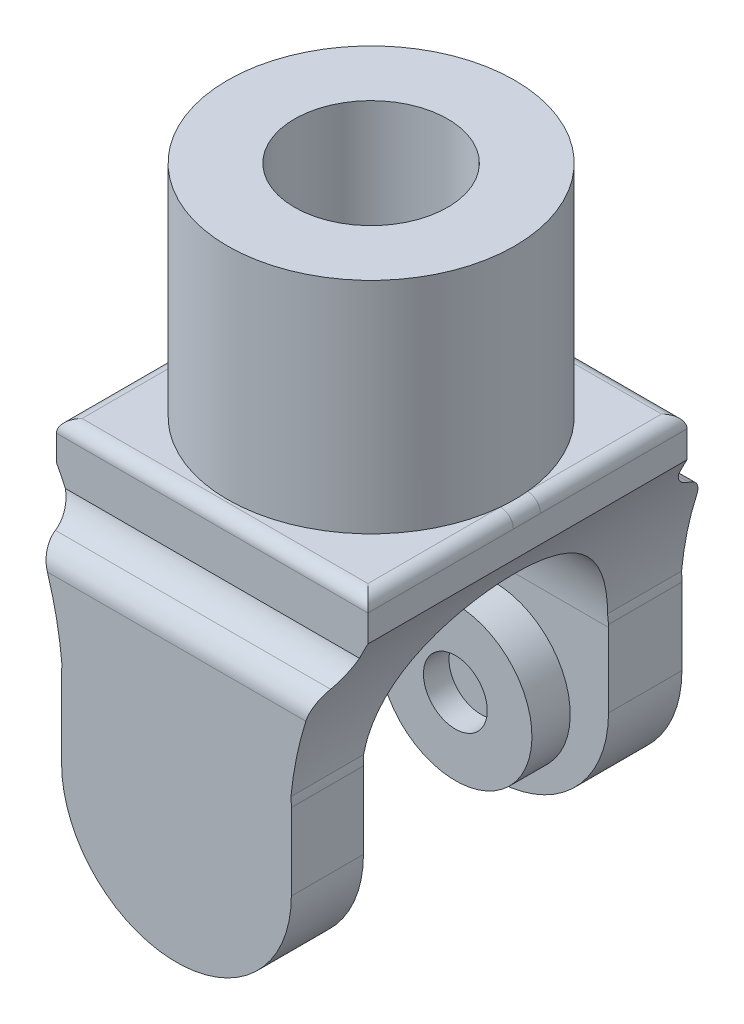
SolidWorks part; units mm, degrees
ref_plane "Front Plane" through (0, 0, 0) normal (0, 0, 1) x (1, 0, 0)
ref_plane "Top Plane" through (0, 0, 0) normal (0, 1, 0) x (1, 0, 0)
ref_plane "Right Plane" through (0, 0, 0) normal (1, 0, 0) x (0, 0, -1)
sketch "Sketch1" plane through (0, 0, 0) normal (0, 1, 0) x (1, 0, 0)
  circle A0 centre (0, 0) radius 14.2875
  circle A1 centre (0, 0) radius 7.62
  dimension "D1" = 28.575
  dimension "D2" = 15.24
extrude "Boss-Extrude1" add sketch "Sketch1" along normal blind 21.844
sketch "Sketch2" plane through (0, 0, 0) normal (0, -1, 0) x (1, 0, 0)
  line L1 (-28.9649, -26.396) -> (28.9649, -26.396)
  line L2 (-28.9649, -26.396) -> (-28.9649, 26.396)
  line L3 (-28.9649, 26.396) -> (28.9649, 26.396)
  line L4 (28.9649, -26.396) -> (28.9649, 26.396)
  line L5 (-28.9649, -26.396) -> (28.9649, 26.396) construction
  line L6 (-28.9649, 26.396) -> (28.9649, -26.396) construction
  point P0 (0, 0)
extrude "Boss-Extrude2" add sketch "Sketch2" along normal blind 37.338
sketch "Sketch4" plane through (0, 0, 26.396) normal (0, 0, 1) x (1, 0, 0)
  line L0 (28.9649, 0) -> (-28.9649, 0) construction
  line L1 (-15.494, 0) -> (15.494, 0)
  line L2 (-15.494, 0) -> (-15.494, -3.81)
  line L3 (-15.494, -37.338) -> (15.494, -37.338)
  line L4 (15.494, 0) -> (15.494, -3.9388)
  line L5 (28.9649, -37.338) -> (-28.9649, -37.338) construction
  line L6 (-11.43, -25.908) -> (-11.43, -18.288)
  line L7 (11.43, -25.908) -> (11.43, -18.288)
  line L8 (14.2875, 0) -> (14.2875, 21.844) construction
  line L9 (-15.494, 0) -> (-15.494, -3.81)
  line L10 (15.494, 0) -> (15.494, -3.9388)
  line L11 (-15.494, 0) -> (-28.9649, 0)
  line L12 (-28.9649, -37.338) -> (-28.9649, 0) construction
  line L13 (-28.9649, 0) -> (-28.9649, -37.338)
  line L14 (-28.9649, -37.338) -> (-15.494, -37.338)
  line L15 (15.494, -37.338) -> (28.9649, -37.338)
  line L16 (28.9649, -37.338) -> (28.9649, 0)
  line L17 (28.9649, 0) -> (15.494, 0)
  arc A0 (-11.43, -25.908) -> (11.43, -25.908) centre (0, -25.908) ccw
  arc A1 (11.43, -18.288) -> (11.3924, -17.3619) centre (0, -18.288) ccw
  arc A2 (-11.43, -18.288) -> (-11.3924, -17.3619) centre (-46.1775, -16.4141) ccw
  arc A3 (11.43, -18.288) -> (11.3924, -17.3619) centre (46.1775, -16.4141) cw
  arc A4 (-11.3924, -17.3619) -> (-11.43, -18.288) centre (0, -18.288) ccw
  arc A5 (-11.3924, -17.3619) -> (-15.494, -3.81) centre (-46.7972, -20.6808) ccw
  arc A6 (11.3924, -17.3619) -> (15.494, -3.9388) centre (46.7822, -20.8374) cw
  dimension "D3" = 22.86
  dimension "D4" = 22.86
  dimension "D5" = 11.43
  dimension "D6" = 15.494
  dimension "D7" = 15.494
  dimension "D8" = 7.62
  dimension "D9" = 3.81
  dimension "D10" = 35.56
  dimension "D12" = 35.56
  dimension "D1" = 30.988
  dimension "D2" = 1.2065
  dimension "D11" = 3.9388
extrude "Cut-Extrude2" cut sketch "Sketch4" against normal through all contours A4 A5 L2 L0 L5 L6 A0 | A6 A1 L7 A0 L3 L6 L0 L4
sketch "Sketch5" plane through (15.494, 0, 0) normal (1, 0, 0) x (0, 0, -1)
  line L1 (-15.8115, 0) -> (15.9385, 0)
  line L2 (-19.3675, -7.9375) -> (-19.3675, -37.338)
  line L3 (-19.3675, -37.338) -> (19.4945, -37.338)
  line L4 (19.4945, -7.9375) -> (19.4945, -37.338)
  line L5 (-26.396, -37.338) -> (26.396, -37.338) construction
  line L6 (14.2875, 0) -> (14.2875, 21.844) construction
  line L7 (-12.192, -18.542) -> (-12.192, -37.338)
  line L8 (-15.8115, 0) -> (15.9385, 0)
  line L9 (-15.8115, 0) -> (-15.8115, -5.588)
  line L11 (15.9385, 0) -> (15.9385, -5.588)
  line L12 (-12.192, -37.338) -> (12.192, -37.338)
  line L13 (12.192, -37.338) -> (12.192, -18.542)
  line L14 (-15.8115, 0) -> (-26.396, 0)
  line L15 (-26.396, 0) -> (-26.396, -37.338)
  line L16 (-26.396, -25.908) -> (-26.396, -37.338) construction
  line L17 (-26.396, -37.338) -> (-12.192, -37.338)
  line L18 (12.192, -37.338) -> (26.396, -37.338)
  line L19 (26.396, -37.338) -> (26.396, 0)
  line L20 (26.396, 0) -> (15.9385, 0)
  arc A0 (-15.8115, -5.588) -> (-19.3675, -7.9375) centre (-18.902, -4.7763) cw
  arc A1 (15.9385, -5.588) -> (19.4945, -7.9375) centre (19.1069, -4.6583) ccw
  arc A2 (12.192, -18.542) -> (-12.192, -18.542) centre (0, -18.542) ccw
  line M7 (-26.396, 0) -> (-26.396, -3.9388)
  line M8 (-26.396, -3.9388) -> (26.396, -3.9388)
  line M9 (26.396, -3.9388) -> (26.396, 0)
  line M10 (26.396, 0) -> (-26.396, 0)
  dimension "D7" = 3.1953
  dimension "D8" = 3.302
  dimension "D5" = 24.384
  dimension "D10" = 18.542
  dimension "D1" = 38.862
  dimension "D2" = 5.207
  dimension "D3" = 31.75
  dimension "D4" = 1.651
  dimension "D6" = 7.9375
  dimension "D9" = 7.9375
extrude "Cut-Extrude3" cut sketch "Sketch5" against normal blind 37.338 contours A0 L9 L15 L17 L2 M8 | L9 M10 M7 M8 | L13 A2 L7 L3 | L11 M10 M8 M9 | L11 A1 L4 L18 L19 M8
fillet "Fillet2" radius 2.54 2 edges at (0.0228, -7.9375, -19.4945) (0.0228, -7.9375, 19.3675)
sketch "Sketch6" plane through (0, 0, 0) normal (0, 1, 0) x (1, 0, 0)
  circle A0 centre (0, 0) radius 7.62
extrude "Cut-Extrude4" cut sketch "Sketch6" against normal blind 37.338
sketch "Sketch7" plane through (0, 0, 12.192) normal (0, 0, -1) x (-1, 0, 0)
  line L0 (11.43, -18.542) -> (-11.43, -18.542) construction
  line L1 (-11.43, -18.542) -> (-11.43, -25.908) construction
  circle A0 centre (0, -27.94) radius 7.62
  dimension "D1" = 15.24
  dimension "D2" = 9.398
  dimension "D3" = 11.43
extrude "Boss-Extrude3" add sketch "Sketch7" along normal blind 3.81
mirror "Mirror1" about plane through (0, 0, 0) normal (0, 0, 1) of "Boss-Extrude3"
sketch "Sketch8" plane through (0, 0, 8.382) normal (0, 0, -1) x (-1, 0, 0)
  circle A0 centre (0, -27.94) radius 3.175
  dimension "D1" = 6.35
extrude "Cut-Extrude5" cut sketch "Sketch8" against normal blind 2.54
mirror "Mirror2" about plane through (0, 0, 0) normal (0, 0, 1) of "Cut-Extrude5"
fillet "Fillet8" radius 1.27 4 edges at (0, 0, -15.9385) (-15.494, 0, -0.0635) (0, 0, 15.8115) (15.494, 0, -0.0635)
